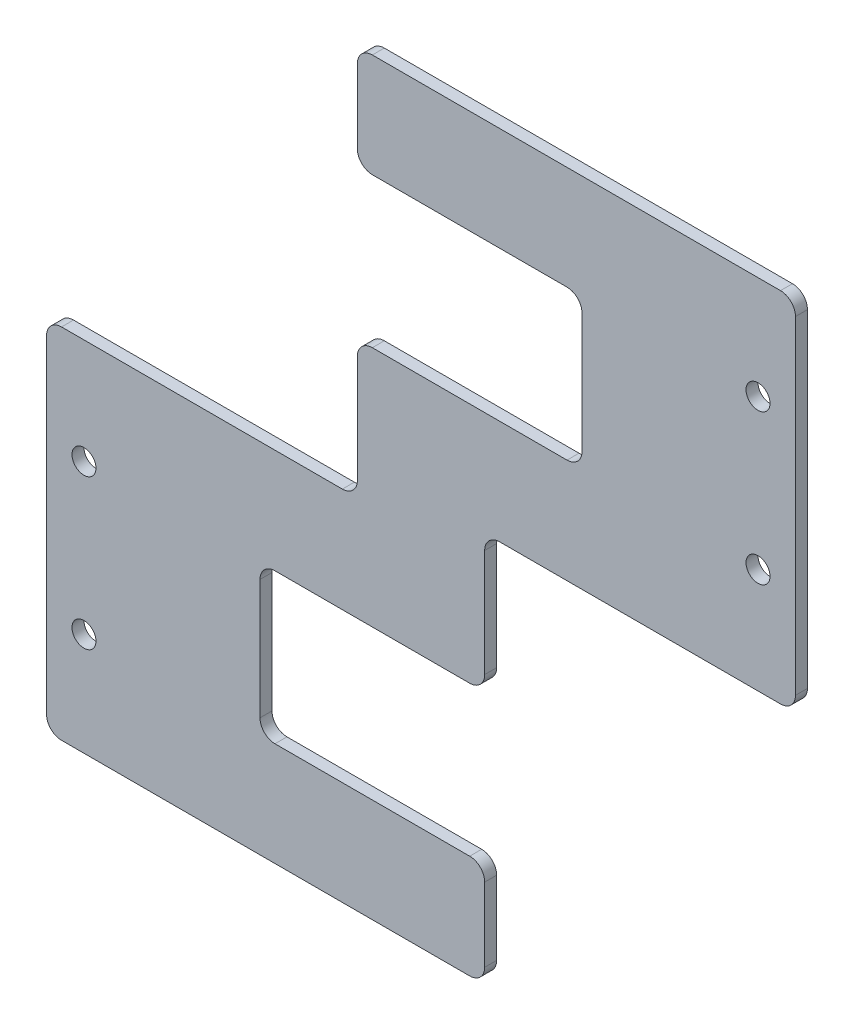
SolidWorks part; units mm, degrees
ref_plane "前视基准面" through (0, 0, 0) normal (0, 0, 1) x (1, 0, 0)
ref_plane "上视基准面" through (0, 0, 0) normal (0, 1, 0) x (1, 0, 0)
ref_plane "右视基准面" through (0, 0, 0) normal (1, 0, 0) x (0, 0, -1)
sketch "草图1" plane through (0, 0, 0) normal (0, 0, 1) x (1, 0, 0)
  line L1 (52.5, -52.5) -> (52.5, 52.5) construction
  line L2 (52.5, 52.5) -> (-52.5, 52.5) construction
  line L4 (-52.5, -52.5) -> (-52.5, 52.5) construction
  line L5 (52.5, -52.5) -> (-52.5, -52.5) construction
  line L7 (-52.5, -52.5) -> (-52.5, -0.2) construction
  line L8 (52.5, 0.2) -> (10.5, 0.2) construction
  line L9 (-52.5, -0.2) -> (-10.5, -0.2) construction
  line L13 (-10.5, 52.5) -> (52.5, 52.5) construction
  line L14 (52.5, 52.5) -> (52.5, 0.2) construction
  line L15 (-52.5, -52.5) -> (10.5, -52.5) construction
  line L16 (10.5, 0.2) -> (10.5, -52.5) construction
  line L17 (-10.5, -0.2) -> (-10.5, 52.5) construction
  line L21 (8.5, 2.2) -> (8.5, -16.15)
  line L25 (-8.5, -2.2) -> (-8.5, 16.15)
  line L26 (21.5, 36.15) -> (-8.5, 36.15)
  line L28 (-21.5, -36.15) -> (-21.5, -16.15)
  line L29 (-21.5, -16.15) -> (8.5, -16.15)
  line L30 (-21.5, -36.15) -> (8.5, -36.15)
  line L31 (21.5, 36.15) -> (21.5, 16.15)
  line L32 (8.5, 2.2) -> (8.5, -50.5) construction
  line L33 (21.5, 16.15) -> (-8.5, 16.15)
  line L34 (-8.5, 36.15) -> (-8.5, 50)
  line L35 (8.5, 2.2) -> (50, 2.2)
  line L36 (-8.5, -2.2) -> (-8.5, 50.5) construction
  line L37 (50.5, 50.5) -> (50.5, 2.2) construction
  line L38 (50.5, 2.2) -> (8.5, 2.2) construction
  line L39 (50, 2.2) -> (50, 50)
  line L40 (50, 50) -> (-8.5, 50)
  line L41 (-8.5, 50.5) -> (50.5, 50.5) construction
  line L42 (-50, -50) -> (8.5, -50)
  line L43 (-50.5, -50.5) -> (-50.5, -2.2) construction
  line L44 (-50.5, -2.2) -> (-8.5, -2.2) construction
  line L45 (-50.5, -50.5) -> (8.5, -50.5) construction
  line L46 (-50, -2.2) -> (-50, -50)
  line L47 (-8.5, -2.2) -> (-50, -2.2)
  line L48 (8.5, -36.15) -> (8.5, -50)
  circle A0 centre (-45, -36.25) radius 1.6
  circle A1 centre (-45, -16.25) radius 1.6
  circle A2 centre (45, 16.25) radius 1.6
  circle A3 centre (45, 36.25) radius 1.6
  point P9 (-52.5, 0)
  point P30 (0, 0)
  point P39 (0, 0)
  point P48 (0, 0)
  dimension "D3" = 2
  dimension "D1" = 2
  dimension "D2" = 2
  dimension "D4" = 2
extrude "凸台-拉伸1" add sketch "草图1" along normal blind 1.6
fillet "圆角1" radius 2 16 edges at (-21.5, -36.15, 0.8) (-21.5, -16.15, 0.8) (8.5, -16.15, 0.8) (-8.5, 36.15, 0.8) (21.5, 36.15, 0.8) (21.5, 16.15, 0.8) (-8.5, 16.15, 0.8) (-8.5, 50, 0.8) (50, 50, 0.8) (8.5, 2.2, 0.8) (50, 2.2, 0.8) (-8.5, -2.2, 0.8) (8.5, -50, 0.8) (8.5, -36.15, 0.8) (-50, -50, 0.8) (-50, -2.2, 0.8)
